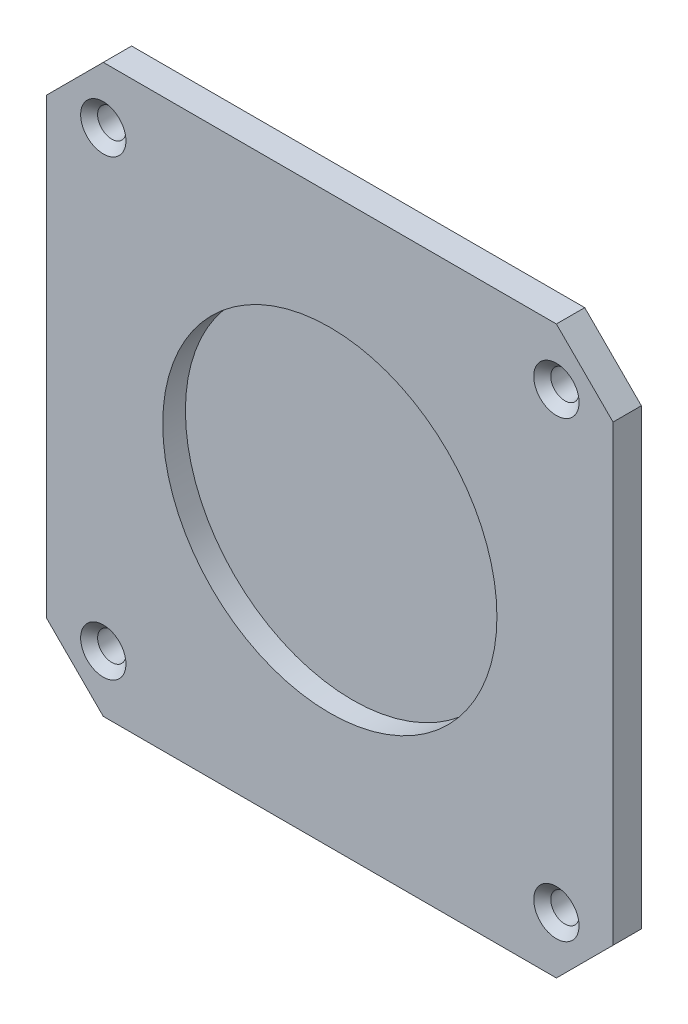
SolidWorks part; units mm, degrees
ref_plane "정면" through (0, 0, 0) normal (0, 0, 1) x (1, 0, 0)
ref_plane "평면" through (0, 0, 0) normal (0, 1, 0) x (1, 0, 0)
ref_plane "우측면" through (0, 0, 0) normal (1, 0, 0) x (0, 0, -1)
sketch "스케치1" plane through (0, 0, 0) normal (0, 0, 1) x (1, 0, 0)
  line L0 (-50, 40) -> (-40, 50)
  line L1 (-40, -50) -> (40, -50)
  line L2 (-50, -40) -> (-50, 40)
  line L3 (-40, 50) -> (40, 50)
  line L4 (50, -40) -> (50, 40)
  line L5 (0, 50) -> (0, -50) construction
  line L6 (-50, 0) -> (50, 0) construction
  line L7 (-50, -40) -> (-40, -50)
  line L8 (40, 50) -> (50, 40)
  line L9 (40, -50) -> (50, -40)
  point P0 (0, 0)
  point P1 (50, 50)
  point P2 (-50, -50)
  point P3 (-50, 50)
  point P124 (50, -50)
  dimension "D1" = 100
  dimension "D2" = 100
extrude "보스-돌출1" add sketch "스케치1" along normal blind 5
sketch "스케치2" plane through (0, 0, 5) normal (0, 0, 1) x (1, 0, 0)
  circle A0 centre (0, 0) radius 29.5
  dimension "D1" = 59
extrude "컷-돌출1" cut sketch "스케치2" against normal blind 4
sketch "스케치3" plane through (0, 0, 5) normal (0, 0, 1) x (1, 0, 0)
  line L6 (-40, -40) -> (40, -40) construction
  line L7 (-40, 40) -> (-40, -40) construction
  line L8 (-40, 40) -> (40, 40) construction
  line L9 (40, 40) -> (40, -40) construction
  dimension "D1" = 80
  dimension "D2" = 80
hole_wizard "M4 납작 십자머리 나사용 카운터싱크1" positions "3D스케치1" profile "스케치5" countersink size "M4" standard "KS" end condition up to next
sketch3d "3D스케치1"
  point P0 (-40, 40, 5)
  point P3 (40, 40, 5)
  point P6 (40, -40, 5)
  point P9 (-40, -40, 5)
sketch "스케치5" plane through (-40, 40, 5) normal (1, 0, 0) x (0, -1, 0)
  line L0 (0, 0) -> (0, 5)
  line L1 (0, 5) -> (2.5, 5)
  line L2 (2.5, 5) -> (2.5, 1.5)
  line L3 (2.5, 1.5) -> (4, 0)
  line L5 (4, 0) -> (0, 0)
  line L6 (-2.5, 1.5) -> (-4, 0) construction
  line L11 (0, -6.35) -> (0, 107.95) construction
  dimension "관통 구멍 지름" = 5
  dimension "관통 구멍 깊이" = 5
  dimension "표면 카운터싱크 지름" = 8
  dimension "표면 카운터싱크 각도" = 90
